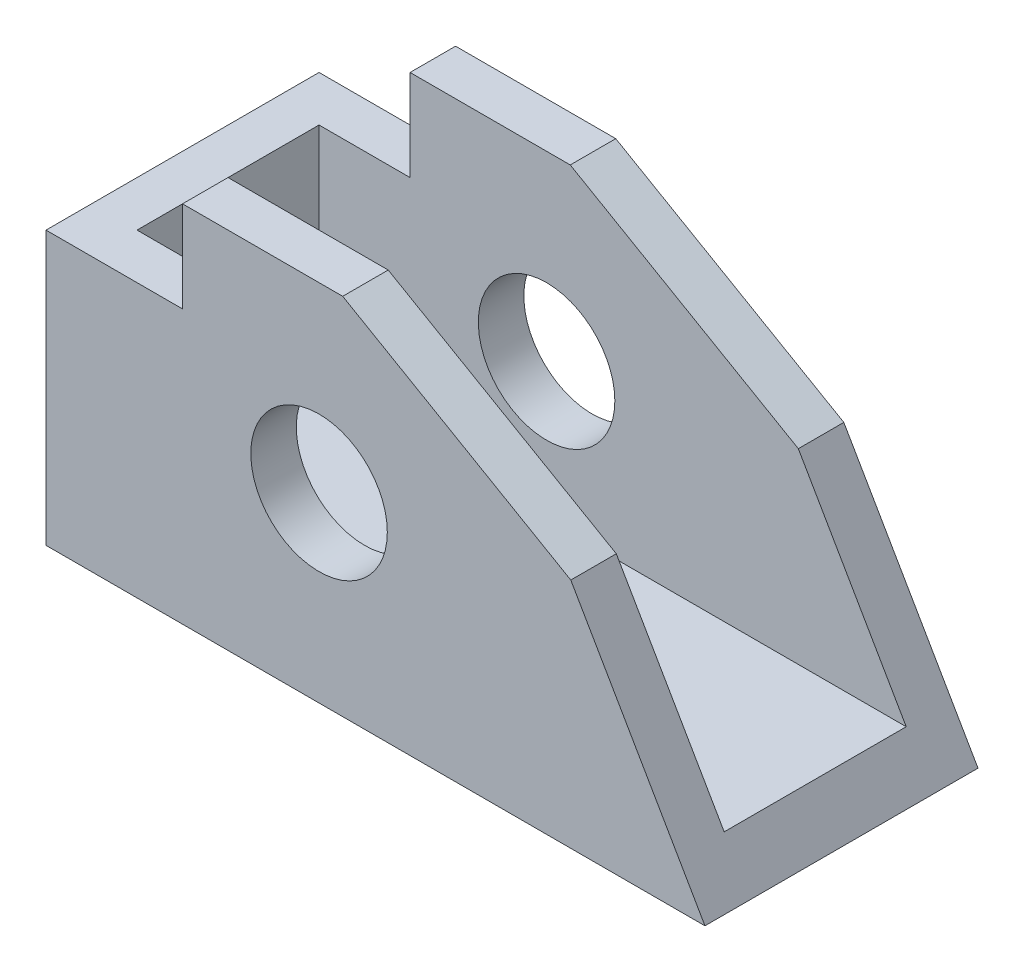
SolidWorks part; units mm, degrees
ref_plane "Front Plane" through (0, 0, 0) normal (0, 0, 1) x (1, 0, 0)
ref_plane "Top Plane" through (0, 0, 0) normal (0, 1, 0) x (1, 0, 0)
ref_plane "Right Plane" through (0, 0, 0) normal (1, 0, 0) x (0, 0, -1)
sketch "Sketch1" plane through (0, 0, 0) normal (0, 1, 0) x (1, 0, 0)
  line L1 (-90.3514, 44.7675) -> (1.5966, 44.7675)
  line L2 (-90.3514, 44.7675) -> (-90.3514, 6.6675)
  line L3 (-90.3514, 6.6675) -> (1.5966, 6.6675)
  line L4 (1.5966, 44.7675) -> (1.5966, 6.6675)
  dimension "D1" = 38.1
  dimension "D2" = 91.948
extrude "Rec : 1.5 x 2.0 x 3.62" add sketch "Sketch1" along normal blind 50.8
sketch "0.5 x 0.75" plane through (0, 0, -6.6675) normal (0, 0, 1) x (1, 0, 0)
  line L1 (-90.3514, 50.8) -> (-71.3014, 50.8)
  line L2 (-90.3514, 50.8) -> (-90.3514, 38.1)
  line L3 (-90.3514, 38.1) -> (-71.3014, 38.1)
  line L4 (-71.3014, 50.8) -> (-71.3014, 38.1)
  dimension "D1" = 12.7
  dimension "D2" = 19.05
sketch "1.0 x 1.75" plane through (1.5966, 0, 0) normal (1, 0, 0) x (0, 0, -1)
  line L0 (6.6675, 50.8) -> (44.7675, 50.8) construction
  line L1 (13.0175, 50.8) -> (38.4175, 50.8)
  line L2 (13.0175, 50.8) -> (13.0175, 6.35)
  line L3 (13.0175, 6.35) -> (38.4175, 6.35)
  line L4 (38.4175, 50.8) -> (38.4175, 6.35)
  line L5 (6.6675, 50.8) -> (6.6675, 0) construction
  line L6 (44.7675, 50.8) -> (44.7675, 0) construction
  line L7 (6.6675, 0) -> (44.7675, 0) construction
  point P8 (13.0175, 28.575)
  point P11 (25.7175, 6.35)
  dimension "D1" = 6.35
  dimension "D2" = 6.35
  dimension "D3" = 6.35
extrude "Rec : 1.0 x 1.75 x 3.37" cut sketch "1.0 x 1.75" against normal blind 85.598
extrude "Rec : 0.5 x 0.75 x 1.5" cut sketch "0.5 x 0.75" against normal through all
sketch "Sketch7" plane through (0, 0, -6.6675) normal (0, 0, 1) x (1, 0, 0)
  line L0 (1.5966, 0) -> (-17.1245, 32.4259)
  line L1 (-17.1245, 32.4259) -> (-48.9494, 50.8)
  line L2 (-71.3014, 50.8) -> (1.5966, 50.8) construction
  line L3 (-48.9494, 50.8) -> (1.5966, 50.8)
  line L4 (1.5966, 50.8) -> (1.5966, 0)
  line L6 (-90.3514, 0) -> (1.5966, 0) construction
  dimension "D1" = 60
  dimension "D2" = 41.402
  dimension "D3" = 30
extrude "Cut-Extrude4" cut sketch "Sketch7" against normal through all
sketch "Sketch8" plane through (0, 0, -6.6675) normal (0, 0, 1) x (1, 0, 0)
  line L0 (-90.3514, 0) -> (1.5966, 0) construction
  line L1 (-90.3514, 38.1) -> (-90.3514, 0) construction
  circle A2 centre (-52.2514, 25.4) radius 9.525
  dimension "D1" = 19.05
  dimension "D2" = 25.4
  dimension "D3" = 38.1
extrude "Cut-Extrude5" cut sketch "Sketch8" against normal through all
